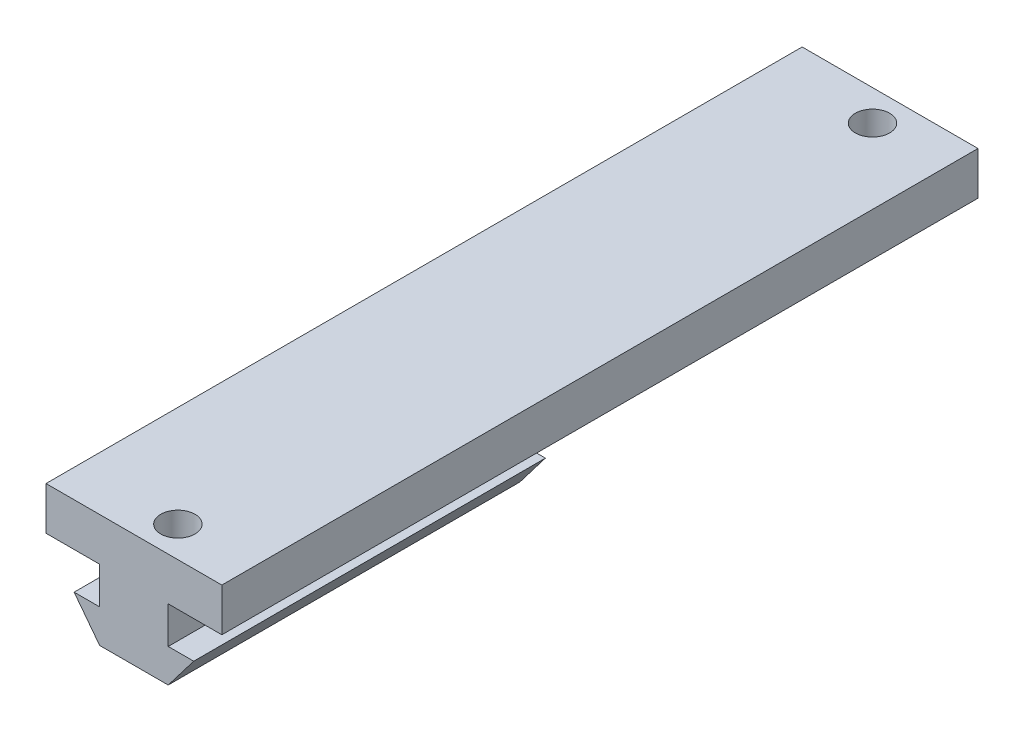
SolidWorks part; units mm, degrees
ref_plane "Front Plane" through (0, 0, 0) normal (0, 0, 1) x (1, 0, 0)
ref_plane "Top Plane" through (0, 0, 0) normal (0, 1, 0) x (1, 0, 0)
ref_plane "Right Plane" through (0, 0, 0) normal (1, 0, 0) x (0, 0, -1)
sketch "Sketch1" plane through (0, 0, 0) normal (0, 1, 0) x (1, 0, 0)
  line L1 (-10, -43) -> (10, -43)
  line L2 (-10, -43) -> (-10, 43)
  line L3 (-10, 43) -> (10, 43)
  line L4 (10, -43) -> (10, 43)
  line L5 (-10, -43) -> (10, 43) construction
  line L6 (-10, 43) -> (10, -43) construction
  point P0 (0, 0)
  dimension "D1" = 20
  dimension "D2" = 86
extrude "Boss-Extrude1" add sketch "Sketch1" along normal blind 4.9
sketch "Sketch2" plane through (0, 4.9, 0) normal (0, 1, 0) x (1, 0, 0)
  line L0 (10, 0) -> (-10, 0) construction
  line L1 (10, -43) -> (10, 43) construction
  line L2 (-10, 43) -> (-10, -43) construction
  circle A0 centre (1.5, -39.5) radius 1.95
  circle A1 centre (1.5, 39.5) radius 1.95
  dimension "D1" = 3.9
  dimension "D2" = 11.5
  dimension "D3" = 79
sketch "Sketch4" plane through (0, 0, 43) normal (0, 0, 1) x (1, 0, 0)
  line L0 (0, 0) -> (0, -2.9) construction
  line L1 (-3.9, 0) -> (-3.9, -4.2)
  line L2 (-10, 0) -> (10, 0) construction
  line L3 (-3.9, -4.2) -> (-6.8, -4.2)
  line L4 (-6.8, -4.2) -> (-3.9, -8)
  line L5 (-3.9, -8) -> (3.9, -8)
  line L6 (3.9, -8) -> (6.8, -4.2)
  line L7 (6.8, -4.2) -> (3.9, -4.2)
  line L8 (3.9, -4.2) -> (3.9, 0)
  line L9 (-3.9, 0) -> (3.9, 0)
  line L10 (0, 4.9) -> (0, -8) construction
  line L11 (-10, 4.9) -> (10, 4.9) construction
  dimension "D1" = 7.8
  dimension "D2" = 2.9
  dimension "D3" = 4.2
  dimension "D4" = 3.8
extrude "Boss-Extrude4" add sketch "Sketch4" against normal blind 40
extrude "Cut-Extrude1" cut sketch "Sketch2" against normal blind 6
